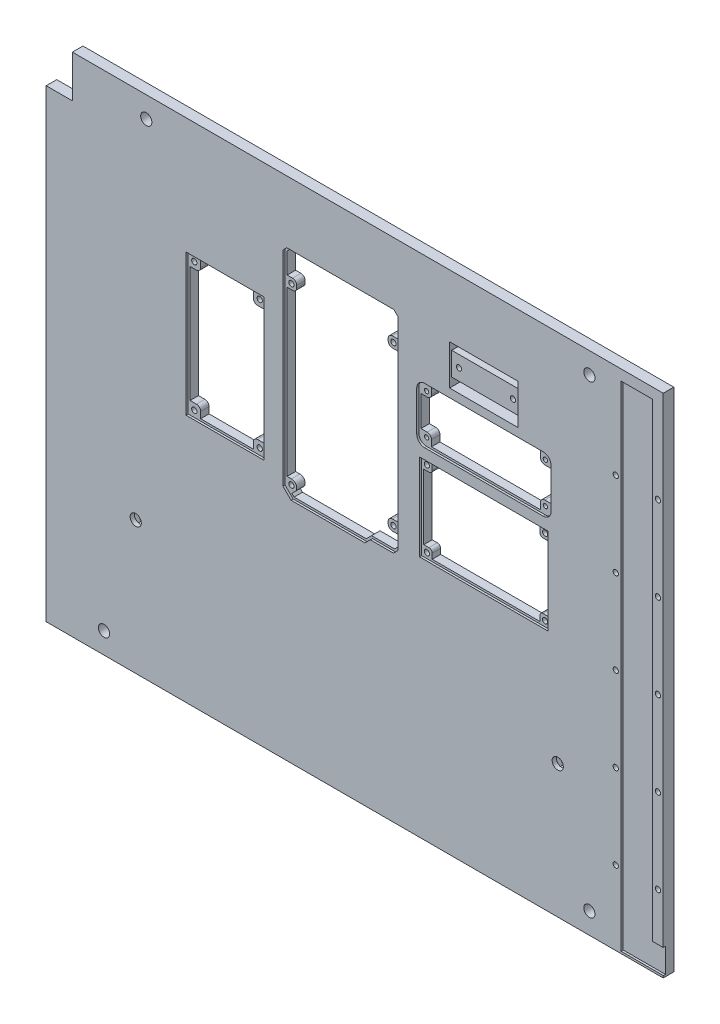
SolidWorks part; units mm, degrees
ref_plane "Front Plane" through (0, 0, 0) normal (0, 0, 1) x (1, 0, 0)
ref_plane "Top Plane" through (0, 0, 0) normal (0, 1, 0) x (1, 0, 0)
ref_plane "Right Plane" through (0, 0, 0) normal (1, 0, 0) x (0, 0, -1)
sketch "Sketch1" plane through (0, 0, 0) normal (0, 0, 1) x (1, 0, 0)
  line L1 (0, 0) -> (300, 0)
  line L2 (0, 0) -> (0, 220)
  line L3 (0, 220) -> (300, 220)
  line L4 (300, 0) -> (300, 220)
  dimension "D1" = 220
  dimension "D2" = 300
extrude "Boss-Extrude1" add sketch "Sketch1" along normal blind 5
sketch "Sketch5" plane through (0, 220, 0) normal (0, 1, 0) x (1, 0, 0)
  line L0 (20, 0) -> (0, 0) construction
  line L1 (20, 0) -> (300, 0)
  line L2 (20, 0) -> (20, -5)
  line L3 (20, -5) -> (300, -5)
  line L4 (300, 0) -> (300, -5)
  line L5 (300, -5) -> (300, 0) construction
  line L6 (20, -5) -> (0, -5) construction
  line L7 (0, -5) -> (0, 0) construction
  dimension "D1" = 20
extrude "Boss-Extrude3" add sketch "Sketch5" along normal blind 20
sketch "Sketch2" plane through (0, 0, 5) normal (0, 0, 1) x (1, 0, 0)
  line L11 (20, 240) -> (300, 240) construction
  line L18 (215, 187) -> (215, 161.6) construction
  line L19 (186.855, 187) -> (243.145, 187)
  line L20 (183.685, 183.83) -> (183.685, 164.77)
  line L21 (186.855, 161.6) -> (243.145, 161.6)
  line L22 (246.315, 183.83) -> (246.315, 164.77)
  line L23 (183.685, 174.3) -> (246.315, 174.3) construction
  line L24 (199.25, 201) -> (230.75, 201) construction
  line L25 (199.25, 192) -> (230.75, 192)
  line L26 (199.25, 192) -> (199.25, 210)
  line L27 (199.25, 210) -> (230.75, 210)
  line L28 (230.75, 192) -> (230.75, 210)
  line L29 (215, 210) -> (215, 192) construction
  line L37 (300, 0) -> (300, 240) construction
  arc A17 (243.145, 187) -> (246.315, 183.83) centre (243.145, 183.83) cw
  arc A18 (246.315, 164.77) -> (243.145, 161.6) centre (243.145, 164.77) cw
  arc A19 (186.855, 161.6) -> (183.685, 164.77) centre (186.855, 164.77) cw
  arc A20 (183.685, 183.83) -> (186.855, 187) centre (186.855, 183.83) cw
  circle A21 centre (186.865, 183.82) radius 1.25
  circle A22 centre (243.135, 183.82) radius 1.25
  circle A23 centre (243.135, 164.78) radius 1.25
  circle A24 centre (186.865, 164.78) radius 1.25
  circle A25 centre (202.2, 201) radius 1.5
  circle A26 centre (227.8, 201) radius 1.5
  point P44 (246.315, 187)
  point P49 (183.685, 161.6)
  point P52 (183.685, 187)
  line B0 (171.9216, 110.94) -> (173.685, 112.7034)
  line B1 (173.685, 112.7034) -> (173.685, 208.476)
  line B2 (173.685, 208.476) -> (172.161, 210)
  line B3 (172.161, 210) -> (121.7928, 210)
  line B4 (121.7928, 210) -> (120.2688, 208.476)
  line B5 (120.2688, 208.476) -> (120.2688, 111.956)
  line B6 (120.2688, 111.956) -> (123.8248, 108.4)
  line B7 (123.8248, 108.4) -> (158.445, 108.4)
  line B8 (158.445, 108.4) -> (160.985, 110.94)
  line B9 (160.985, 110.94) -> (171.9216, 110.94)
  circle B10 centre (122.8088, 113.2514) radius 1.5621
  circle B11 centre (122.8088, 195.8776) radius 1.5621
  circle B12 centre (171.145, 195.8776) radius 1.5621
  circle B13 centre (171.145, 120.7444) radius 1.5621
  line B14 (74.2688, 151.4) -> (110.2688, 151.4) construction
  line B15 (74.2688, 118.4) -> (74.2688, 184.4)
  line B16 (74.2688, 118.4) -> (110.2688, 118.4)
  line B17 (110.2688, 118.4) -> (110.2688, 184.4)
  line B18 (74.2688, 184.4) -> (110.2688, 184.4)
  line B19 (92.2688, 118.4) -> (92.2688, 184.4) construction
  circle B20 centre (76.7688, 120.9) radius 1.6
  circle B21 centre (76.7688, 181.9) radius 1.6
  circle B22 centre (107.7688, 181.9) radius 1.6
  circle B23 centre (107.7688, 120.9) radius 1.6
  line B24 (275, 12.5) -> (275, 0)
  line B25 (275, 240) -> (300, 240)
  line B26 (275, 240) -> (275, 12.5)
  line B27 (275, 12.5) -> (300, 12.5) construction
  line B28 (295, 217.7) -> (280, 217.7) construction
  line B29 (295, 12.5) -> (295, 217.7) construction
  line B30 (280, 12.5) -> (295, 12.5) construction
  line B31 (280, 217.7) -> (280, 12.5) construction
  line B32 (300, 240) -> (300, 12.5)
  line B33 (275, 0) -> (300, 0)
  line B34 (300, 0) -> (300, 12.5)
  circle B35 centre (297.5, 35.1) radius 1.25
  circle B36 centre (297.5, 75.1) radius 1.25
  circle B37 centre (297.5, 115.1) radius 1.25
  circle B38 centre (297.5, 155.1) radius 1.25
  circle B39 centre (297.5, 195.1) radius 1.25
  circle B40 centre (277.5, 195.1) radius 1.25
  circle B41 centre (277.5, 155.1) radius 1.25
  circle B42 centre (277.5, 75.1) radius 1.25
  circle B43 centre (277.5, 115.1) radius 1.25
  circle B44 centre (277.5, 35.1) radius 1.25
  dimension "D37" = 3.17
  dimension "D38" = 2.5
  dimension "D39" = 3.18
  dimension "D40" = 3.18
  dimension "D45" = 3
  dimension "D1" = 30
  dimension "D2" = 10
  dimension "D5" = 10
  dimension "D6" = 5
  dimension "D7" = 25.6
  dimension "D8" = 10
  dimension "D35" = 62.63
  dimension "D36" = 25.4
  dimension "D41" = 85
  dimension "D43" = 31.5
  dimension "D44" = 18
sketch_block_instance "Block1-1"
sketch_block "Block1" parameters "D8"=1.5621, "D15"=1.5621, "D16"=1.5621, "D19"=3.1242, "D1"=2.54, "D2"=2.54, "D3"=9.8044, "D4"=2.54, "D5"=2.54, "D6"=14.1224, "D7"=14.1224, "D9"=53.4162, "D10"=101.6, "D11"=99.06, "D12"=3.5921, "D13"=5.0289, "D14"=2.4939, "D17"=2.1553, "D18"=2.1553, "D20"=34.6202, "D21"=10.9366, "D22"=4.8514, "D23"=1.524, "D24"=3.556, "D25"=1.524
sketch_block_instance "Block4-1"
sketch_block "Block4" parameters "D3"=3.2, "D1"=66, "D2"=36, "D4"=2.5, "D5"=2.5
sketch_block_instance "Block5-1"
sketch_block "Block5" parameters "D1"=25, "D2"=227.5, "D3"=12.5
sketch "Sketch7" plane through (0, 0, 5) normal (0, 0, 1) x (1, 0, 0)
  line L0 (295, 12.5) -> (300, 12.5)
  line L1 (300, 12.5) -> (300, 1)
  line L2 (300, 0) -> (300, 12.5) construction
  line L187 (119.7688, 111.7489) -> (123.6177, 107.9)
  line L188 (123.6177, 107.9) -> (158.6521, 107.9)
  line L189 (158.6521, 107.9) -> (161.1921, 110.44)
  line L190 (161.1921, 110.44) -> (172.1287, 110.44)
  line L191 (172.1287, 110.44) -> (174.185, 112.4963)
  line L192 (174.185, 112.4963) -> (174.185, 208.6831)
  line L193 (174.185, 208.6831) -> (172.3681, 210.5)
  line L194 (119.7688, 208.6831) -> (119.7688, 111.7489)
  line L195 (121.5857, 210.5) -> (119.7688, 208.6831)
  line L196 (172.3681, 210.5) -> (121.5857, 210.5)
  line L197 (119.7688, 111.7489) -> (123.6177, 107.9)
  line L198 (123.6177, 107.9) -> (158.6521, 107.9)
  line L199 (158.6521, 107.9) -> (161.1921, 110.44)
  line L200 (161.1921, 110.44) -> (172.1287, 110.44)
  line L201 (172.1287, 110.44) -> (174.185, 112.4963)
  line L202 (174.185, 112.4963) -> (174.185, 208.6831)
  line L203 (174.185, 208.6831) -> (172.3681, 210.5)
  line L204 (119.7688, 208.6831) -> (119.7688, 111.7489)
  line L205 (121.5857, 210.5) -> (119.7688, 208.6831)
  line L206 (172.3681, 210.5) -> (121.5857, 210.5)
  line L211 (110.7688, 117.9) -> (110.7688, 184.9)
  line L212 (73.7688, 117.9) -> (110.7688, 117.9)
  line L213 (73.7688, 184.9) -> (73.7688, 117.9)
  line L214 (110.7688, 184.9) -> (73.7688, 184.9)
  line L215 (110.7688, 117.9) -> (110.7688, 184.9)
  line L216 (73.7688, 117.9) -> (110.7688, 117.9)
  line L217 (73.7688, 184.9) -> (73.7688, 117.9)
  line L218 (110.7688, 184.9) -> (73.7688, 184.9)
  line L223 (243.145, 187.5) -> (186.855, 187.5)
  line L224 (246.815, 164.77) -> (246.815, 183.83)
  line L225 (186.855, 161.1) -> (243.145, 161.1)
  line L226 (183.185, 183.83) -> (183.185, 164.77)
  line L227 (243.145, 187.5) -> (186.855, 187.5)
  line L228 (246.815, 164.77) -> (246.815, 183.83)
  line L229 (186.855, 161.1) -> (243.145, 161.1)
  line L230 (183.185, 183.83) -> (183.185, 164.77)
  line L231 (300, 1) -> (280, 1)
  line L232 (184.5, 156.1) -> (245.5, 156.1)
  line L233 (184.5, 156.1) -> (184.5, 115.1)
  line L234 (184.5, 115.1) -> (245.5, 115.1)
  line L235 (198.75, 210.5) -> (198.75, 191.5)
  line L236 (198.75, 191.5) -> (231.25, 191.5)
  line L237 (231.25, 191.5) -> (231.25, 210.5)
  line L238 (231.25, 210.5) -> (198.75, 210.5)
  line L239 (198.75, 210.5) -> (198.75, 191.5)
  line L240 (198.75, 191.5) -> (231.25, 191.5)
  line L241 (231.25, 191.5) -> (231.25, 210.5)
  line L242 (231.25, 210.5) -> (198.75, 210.5)
  line L243 (245.5, 156.1) -> (245.5, 115.1)
  line L244 (184.5, 156.1) -> (245.5, 115.1) construction
  line L245 (184.5, 115.1) -> (245.5, 156.1) construction
  line L247 (280, 1) -> (280, 235)
  line L249 (295, 12.5) -> (295, 235)
  line L250 (295, 12.5) -> (295, 217.7) construction
  line L251 (295, 235) -> (280, 235)
  line L252 (275, 240) -> (300, 240) construction
  line L253 (280, 217.7) -> (280, 12.5) construction
  line L254 (275, 0) -> (300, 0) construction
  line L256 (215, 156.1) -> (215, 115.1) construction
  line L257 (215, 187) -> (215, 161.6) construction
  arc A11 (246.815, 183.83) -> (243.145, 187.5) centre (243.145, 183.83) ccw
  arc A12 (243.145, 161.1) -> (246.815, 164.77) centre (243.145, 164.77) ccw
  arc A13 (183.185, 164.77) -> (186.855, 161.1) centre (186.855, 164.77) ccw
  arc A14 (186.855, 187.5) -> (183.185, 183.83) centre (186.855, 183.83) ccw
  arc A15 (246.815, 183.83) -> (243.145, 187.5) centre (243.145, 183.83) ccw
  arc A16 (243.145, 161.1) -> (246.815, 164.77) centre (243.145, 164.77) ccw
  arc A17 (183.185, 164.77) -> (186.855, 161.1) centre (186.855, 164.77) ccw
  arc A18 (186.855, 187.5) -> (183.185, 183.83) centre (186.855, 183.83) ccw
  point P0 (215, 135.6)
  dimension "D5" = 5
  dimension "D6" = 41
  dimension "D7" = 5
  dimension "D8" = 1
  dimension "D9" = 61
  dimension "D1" = 0.5
  dimension "D2" = 0.5
  dimension "D3" = 0.5
  dimension "D4" = 0.5
extrude "Cut-Extrude3" cut sketch "Sketch7" against normal blind 1
sketch "Sketch9" plane through (0, 0, 5) normal (0, 0, 1) x (1, 0, 0)
  line L0 (79.7688, 183.9) -> (92.2688, 183.9)
  line L1 (73.7688, 184.9) -> (79.7688, 184.9) construction
  line L2 (73.7688, 184.9) -> (73.7688, 178.9) construction
  line L3 (73.7688, 178.9) -> (79.7688, 178.9) construction
  line L4 (79.7688, 184.9) -> (79.7688, 178.9) construction
  line L5 (92.2688, 118.4) -> (92.2688, 184.4) construction
  line L6 (74.7688, 178.9) -> (74.7688, 123.9)
  line L7 (74.2688, 151.4) -> (110.2688, 151.4) construction
  line L8 (73.7688, 184.9) -> (73.7688, 117.9) construction
  line L9 (110.7688, 184.9) -> (73.7688, 184.9) construction
  line L10 (79.7688, 183.9) -> (79.7688, 180.9)
  line L11 (77.7688, 178.9) -> (74.7688, 178.9)
  line L12 (92.2688, 184.9) -> (92.2688, 117.9) construction
  line L13 (110.7688, 184.9) -> (73.7688, 184.9) construction
  line L14 (73.7688, 117.9) -> (110.7688, 117.9) construction
  line L15 (74.2688, 151.4) -> (110.2688, 151.4) construction
  line L16 (74.2688, 118.4) -> (74.2688, 184.4) construction
  line L17 (92.2688, 176.5163) -> (92.2688, 184.9) construction
  line L18 (71.2994, 151.4) -> (74.2688, 151.4) construction
  line L19 (109.7688, 178.9) -> (109.7688, 123.9)
  line L20 (106.7688, 178.9) -> (109.7688, 178.9)
  line L21 (104.7688, 183.9) -> (104.7688, 180.9)
  line L22 (104.7688, 183.9) -> (92.2688, 183.9)
  line L23 (77.7688, 123.9) -> (74.7688, 123.9)
  line L24 (79.7688, 118.9) -> (79.7688, 121.9)
  line L25 (79.7688, 118.9) -> (92.2688, 118.9)
  line L26 (106.7688, 123.9) -> (109.7688, 123.9)
  line L27 (104.7688, 118.9) -> (104.7688, 121.9)
  line L28 (104.7688, 118.9) -> (92.2688, 118.9)
  line L29 (215, 156.1) -> (215, 115.1) construction
  line L34 (245.5, 156.1) -> (184.5, 156.1) construction
  line L35 (120.3088, 193.3776) -> (125.3088, 193.3776) construction
  line L36 (120.3088, 193.3776) -> (120.3088, 198.3776) construction
  line L37 (120.3088, 198.3776) -> (125.3088, 198.3776) construction
  line L38 (125.3088, 193.3776) -> (125.3088, 198.3776) construction
  line L39 (120.3088, 193.3776) -> (125.3088, 198.3776) construction
  line L40 (120.3088, 198.3776) -> (125.3088, 193.3776) construction
  line L41 (173.645, 193.3776) -> (168.645, 193.3776) construction
  line L42 (173.645, 193.3776) -> (173.645, 198.3776) construction
  line L43 (173.645, 198.3776) -> (168.645, 198.3776) construction
  line L44 (168.645, 193.3776) -> (168.645, 198.3776) construction
  line L45 (173.645, 193.3776) -> (168.645, 198.3776) construction
  line L46 (173.645, 198.3776) -> (168.645, 193.3776) construction
  line L47 (173.645, 118.2444) -> (168.645, 118.2444) construction
  line L48 (173.645, 118.2444) -> (173.645, 123.2444) construction
  line L49 (173.645, 123.2444) -> (168.645, 123.2444) construction
  line L50 (168.645, 118.2444) -> (168.645, 123.2444) construction
  line L51 (173.645, 118.2444) -> (168.645, 123.2444) construction
  line L52 (173.645, 123.2444) -> (168.645, 118.2444) construction
  line L57 (184.5, 115.1) -> (245.5, 115.1) construction
  line L58 (184.5, 135.6) -> (245.5, 135.6) construction
  line L59 (184.5, 156.1) -> (184.5, 115.1) construction
  line L60 (245.5, 115.1) -> (245.5, 156.1) construction
  line L61 (185.5, 120.1) -> (185.5, 151.1)
  line L62 (185.5, 151.1) -> (187.9668, 151.1)
  line L63 (189.5, 152.6332) -> (189.5, 155.1)
  line L64 (189.5, 155.1) -> (240.5, 155.1)
  line L65 (245.5, 156.1) -> (184.5, 156.1) construction
  line L66 (240.5, 152.6332) -> (240.5, 155.1)
  line L67 (244.5, 151.1) -> (242.0332, 151.1)
  line L68 (244.5, 120.1) -> (244.5, 151.1)
  line L69 (244.5, 120.1) -> (242.0332, 120.1)
  line L70 (240.5, 118.5668) -> (240.5, 116.1)
  line L71 (189.5, 116.1) -> (240.5, 116.1)
  line L72 (189.5, 118.5668) -> (189.5, 116.1)
  line L73 (185.5, 120.1) -> (187.9668, 120.1)
  line L108 (173.185, 208.2689) -> (173.185, 198.3776)
  line L109 (173.185, 198.3776) -> (170.645, 198.3776)
  line L110 (168.645, 196.3776) -> (168.645, 195.3776)
  line L111 (170.645, 193.3776) -> (173.185, 193.3776)
  line L112 (173.185, 193.3776) -> (173.185, 123.2444)
  line L113 (173.185, 123.2444) -> (170.645, 123.2444)
  line L114 (168.645, 121.2444) -> (168.645, 120.2444)
  line L115 (170.645, 118.2444) -> (173.185, 118.2444)
  line L116 (173.185, 118.2444) -> (173.185, 112.9105)
  line L117 (123.0124, 109.9195) -> (124.5766, 111.4836)
  line L118 (121.9999, 209.5) -> (120.7688, 208.2689)
  line L119 (171.9539, 209.5) -> (121.9999, 209.5)
  line L120 (173.185, 208.2689) -> (171.9539, 209.5)
  line L121 (173.185, 112.9105) -> (173.185, 208.2689)
  line L122 (171.7145, 111.44) -> (173.185, 112.9105)
  line L123 (160.7779, 111.44) -> (171.7145, 111.44)
  line L124 (158.2379, 108.9) -> (160.7779, 111.44)
  line L125 (124.0319, 108.9) -> (158.2379, 108.9)
  line L126 (120.7688, 112.1631) -> (124.0319, 108.9)
  line L127 (120.7688, 208.2689) -> (120.7688, 112.1631)
  line L128 (121.9999, 209.5) -> (120.7688, 208.2689)
  line L129 (171.9539, 209.5) -> (121.9999, 209.5)
  line L130 (173.185, 208.2689) -> (171.9539, 209.5)
  line L131 (173.185, 112.9105) -> (173.185, 208.2689) construction
  line L132 (171.7145, 111.44) -> (173.185, 112.9105)
  line L133 (160.7779, 111.44) -> (171.7145, 111.44)
  line L134 (158.2379, 108.9) -> (160.7779, 111.44)
  line L135 (124.0319, 108.9) -> (158.2379, 108.9)
  line L136 (120.7688, 112.1631) -> (124.0319, 108.9) construction
  line L137 (120.7688, 208.2689) -> (120.7688, 112.1631) construction
  line L138 (120.7688, 115.7514) -> (122.8088, 115.7514)
  line L139 (123.0124, 109.9195) -> (124.0319, 108.9)
  line L140 (120.7688, 115.7514) -> (120.7688, 193.3776)
  line L141 (120.7688, 193.3776) -> (123.3088, 193.3776)
  line L142 (125.3088, 195.3776) -> (125.3088, 196.3776)
  line L143 (123.3088, 198.3776) -> (120.7688, 198.3776)
  line L144 (120.7688, 198.3776) -> (120.7688, 208.2689)
  line L145 (231.25, 191.5) -> (231.25, 210.5) construction
  line L146 (198.75, 210.5) -> (231.25, 210.5)
  line L147 (198.75, 210.5) -> (198.75, 206.5)
  line L148 (198.75, 206.5) -> (231.25, 206.5)
  line L149 (231.25, 210.5) -> (231.25, 206.5)
  line L150 (230.75, 192) -> (230.75, 210) construction
  line L151 (198.75, 191.5) -> (230.75, 191.5)
  line L152 (198.75, 191.5) -> (198.75, 195.5)
  line L153 (198.75, 195.5) -> (230.75, 195.5)
  line L154 (230.75, 191.5) -> (230.75, 195.5)
  line L155 (215, 187) -> (215, 189.4399) construction
  line L156 (183.685, 174.3) -> (181.2405, 174.3) construction
  line L157 (183.685, 183.83) -> (183.685, 164.77) construction
  line L158 (184.185, 167.1) -> (184.185, 181.5)
  line L159 (183.685, 174.3) -> (246.315, 174.3) construction
  line L160 (184.185, 181.5) -> (187.185, 181.5)
  line L161 (189.185, 183.5) -> (189.185, 186.5)
  line L162 (189.185, 186.5) -> (240.815, 186.5)
  line L163 (215, 187) -> (215, 161.6) construction
  line L164 (186.855, 187) -> (243.145, 187) construction
  line L165 (189.185, 162.1) -> (240.815, 162.1)
  line L166 (189.185, 165.1) -> (189.185, 162.1)
  line L167 (184.185, 167.1) -> (187.185, 167.1)
  line L168 (240.815, 165.1) -> (240.815, 162.1)
  line L169 (245.815, 167.1) -> (242.815, 167.1)
  line L170 (245.815, 167.1) -> (245.815, 181.5)
  line L171 (245.815, 181.5) -> (242.815, 181.5)
  line L172 (240.815, 183.5) -> (240.815, 186.5)
  circle A0 centre (76.7688, 181.9) radius 1.25
  arc A1 (79.7688, 180.9) -> (77.7688, 178.9) centre (77.7688, 180.9) cw
  arc A2 (104.7688, 180.9) -> (106.7688, 178.9) centre (106.7688, 180.9) ccw
  arc A3 (79.7688, 121.9) -> (77.7688, 123.9) centre (77.7688, 121.9) ccw
  arc A4 (104.7688, 121.9) -> (106.7688, 123.9) centre (106.7688, 121.9) cw
  circle A5 centre (107.7688, 181.9) radius 1.25
  circle A6 centre (107.7688, 120.9) radius 1.25
  circle A7 centre (76.7688, 120.9) radius 1.25
  circle A8 centre (297.5, 35.1) radius 1.25 construction
  circle A9 centre (277.5, 35.1) radius 1.25 construction
  circle A10 centre (277.5, 75.1) radius 1.25 construction
  circle A11 centre (297.5, 75.1) radius 1.25 construction
  circle A12 centre (297.5, 115.1) radius 1.25 construction
  circle A13 centre (277.5, 115.1) radius 1.25 construction
  circle A14 centre (277.5, 155.1) radius 1.25 construction
  circle A15 centre (297.5, 155.1) radius 1.25 construction
  circle A16 centre (297.5, 195.1) radius 1.25 construction
  circle A17 centre (277.5, 195.1) radius 1.25 construction
  circle A18 centre (297.5, 35.1) radius 1.25
  circle A19 centre (277.5, 35.1) radius 1.25
  circle A20 centre (277.5, 75.1) radius 1.25
  circle A21 centre (297.5, 75.1) radius 1.25
  circle A22 centre (297.5, 115.1) radius 1.25
  circle A23 centre (277.5, 115.1) radius 1.25
  circle A24 centre (277.5, 155.1) radius 1.25
  circle A25 centre (297.5, 155.1) radius 1.25
  circle A26 centre (297.5, 195.1) radius 1.25
  circle A27 centre (277.5, 195.1) radius 1.25
  arc A28 (122.8088, 115.7514) -> (124.5766, 111.4836) centre (122.8088, 113.2514) cw
  circle A29 centre (122.8088, 113.2514) radius 1.5621 construction
  arc A30 (170.645, 118.2444) -> (168.645, 120.2444) centre (170.645, 120.2444) cw
  arc A31 (168.645, 121.2444) -> (170.645, 123.2444) centre (170.645, 121.2444) cw
  arc A32 (168.645, 195.3776) -> (170.645, 193.3776) centre (170.645, 195.3776) ccw
  arc A33 (168.645, 196.3776) -> (170.645, 198.3776) centre (170.645, 196.3776) cw
  arc A34 (125.3088, 195.3776) -> (123.3088, 193.3776) centre (123.3088, 195.3776) cw
  arc A35 (125.3088, 196.3776) -> (123.3088, 198.3776) centre (123.3088, 196.3776) ccw
  circle A36 centre (122.8088, 113.2514) radius 1.25
  circle A37 centre (171.145, 120.7444) radius 1.25
  circle A38 centre (122.8088, 195.8776) radius 1.25
  circle A39 centre (171.145, 195.8776) radius 1.25
  circle A40 centre (202.2, 201) radius 1.25
  circle A41 centre (227.8, 201) radius 1.25
  arc A42 (189.185, 183.5) -> (187.185, 181.5) centre (187.185, 183.5) cw
  arc A43 (189.185, 165.1) -> (187.185, 167.1) centre (187.185, 165.1) ccw
  arc A44 (240.815, 165.1) -> (242.815, 167.1) centre (242.815, 165.1) cw
  arc A45 (240.815, 183.5) -> (242.815, 181.5) centre (242.815, 183.5) ccw
  circle A46 centre (186.865, 183.82) radius 1.025
  circle A47 centre (186.865, 164.78) radius 1.025
  circle A48 centre (243.145, 164.77) radius 1.025
  circle A49 centre (243.135, 183.82) radius 1.025
  circle A50 centre (243.135, 183.82) radius 1.25 construction
  circle A51 centre (186.865, 164.78) radius 1.25 construction
  circle A52 centre (186.865, 183.82) radius 1.25 construction
  circle A53 centre (187, 153.6) radius 1.25
  arc A54 (189.5, 152.6332) -> (187.9668, 151.1) centre (187.9668, 152.6332) cw
  arc A55 (240.5, 152.6332) -> (242.0332, 151.1) centre (242.0332, 152.6332) ccw
  arc A56 (240.5, 118.5668) -> (242.0332, 120.1) centre (242.0332, 118.5668) cw
  arc A57 (189.5, 118.5668) -> (187.9668, 120.1) centre (187.9668, 118.5668) ccw
  circle A58 centre (243, 153.6) radius 1.25
  circle A59 centre (243, 117.6) radius 1.25
  circle A60 centre (187, 117.6) radius 1.25
  point P15 (86.0188, 183.9)
  point P44 (74.7688, 151.4)
  point P50 (109.7688, 151.4)
  point P90 (171.145, 195.8776)
  point P95 (171.145, 120.7444)
  point P97 (122.8088, 195.8776)
  point P107 (122.8088, 113.2514)
  point P198 (189.185, 181.5)
  point P205 (184.185, 174.3)
  point P206 (215, 162.1)
  point P215 (215, 186.5)
  point P254 (215, 155.1)
  point P260 (244.5, 135.6)
  point P269 (185.5, 135.6)
  dimension "D5" = 2.5
  dimension "D6" = 2
  dimension "D7" = 5
  dimension "D10" = 2.5
  dimension "D16" = 2.5
  dimension "D17" = 2
  dimension "D18" = 2.5
  dimension "D19" = 2.5
  dimension "D20" = 2.5
  dimension "D21" = 2.5
  dimension "D24" = 2.5
  dimension "D25" = 2.5
  dimension "D30" = 2
  dimension "D31" = 2.05
  dimension "D32" = 2.05
  dimension "D33" = 2.05
  dimension "D34" = 2.05
  dimension "D35" = 2.5
  dimension "D36" = 2.5
  dimension "D37" = 2.5
  dimension "D42" = 1.5332
  dimension "D1" = 6
  dimension "D2" = 6
  dimension "D3" = 1
  dimension "D4" = 1
  dimension "D8" = 5
  dimension "D9" = 0.5
  dimension "D11" = 5
  dimension "D12" = 5
  dimension "D13" = 5
  dimension "D14" = 5
  dimension "D15" = 2.5
  dimension "D22" = 4
  dimension "D23" = 4
  dimension "D26" = 0.5
  dimension "D27" = 0.5
  dimension "D28" = 5
  dimension "D29" = 5
  dimension "D38" = 5
  dimension "D39" = 5
  dimension "D40" = 1
  dimension "D41" = 1
extrude "Cut-Extrude4" cut sketch "Sketch9" against normal blind 5
sketch "Sketch10" plane through (0, 0, 5) normal (0, 0, 1) x (1, 0, 0)
  line L0 (0, 63) -> (300, 63) construction
  line L1 (0, 220) -> (0, 0) construction
  line L2 (300, 240) -> (300, 12.5) construction
  line L3 (0, 10) -> (300, 10) construction
  line L5 (0, 0) -> (300, 0) construction
  line L6 (20, 230) -> (300, 230) construction
  line L7 (20, 240) -> (20, 220) construction
  circle A0 centre (50, 63) radius 2.65
  circle A1 centre (250, 63) radius 2.65
  circle A2 centre (35, 10) radius 2.65
  circle A3 centre (265, 10) radius 2.65
  circle A4 centre (265, 230) radius 2.65
  circle A5 centre (55, 230) radius 2.65
  dimension "D1" = 5.3
  dimension "D3" = 5.3
  dimension "D5" = 200
  dimension "D6" = 63
  dimension "D7" = 5.3
  dimension "D8" = 5.3
  dimension "D9" = 5.3
  dimension "D10" = 5.3
  dimension "D12" = 35
  dimension "D13" = 35
  dimension "D14" = 35
  dimension "D2" = 50
  dimension "D4" = 10
  dimension "D11" = 35
extrude "Cut-Extrude5" cut sketch "Sketch10" against normal blind 10
sketch "Sketch11" plane through (0, 0, 0) normal (0, 0, -1) x (-1, 0, 0)
  line L0 (0, 0) -> (-300, 0) construction
  line L1 (-247.5174, 67.3) -> (-252.4826, 67.3)
  line L2 (-252.4826, 67.3) -> (-254.9652, 63)
  line L3 (-254.9652, 63) -> (-252.4826, 58.7)
  line L4 (-252.4826, 58.7) -> (-247.5174, 58.7)
  line L5 (-247.5174, 58.7) -> (-245.0348, 63)
  line L6 (-245.0348, 63) -> (-247.5174, 67.3)
  line L8 (-47.5174, 67.3) -> (-52.4826, 67.3)
  line L9 (-52.4826, 67.3) -> (-54.9652, 63)
  line L10 (-54.9652, 63) -> (-52.4826, 58.7)
  line L11 (-52.4826, 58.7) -> (-47.5174, 58.7)
  line L12 (-47.5174, 58.7) -> (-45.0348, 63)
  line L13 (-45.0348, 63) -> (-47.5174, 67.3)
  circle A0 centre (-250, 63) radius 4.3 construction
  circle A1 centre (-50, 63) radius 4.3 construction
  dimension "D1" = 8.6
  dimension "D2" = 8.6
extrude "Cut-Extrude6" cut sketch "Sketch11" against normal blind 3
sketch "Sketch12" plane through (0, 0, 5) normal (0, 0, 1) x (1, 0, 0)
  line L1 (-7.5879, 452.3851) -> (7.5879, 452.3851)
  line L2 (-7.5879, 452.3851) -> (-7.5879, -12.3851)
  line L3 (-7.5879, -12.3851) -> (7.5879, -12.3851)
  line L4 (7.5879, 452.3851) -> (7.5879, -12.3851)
  line L5 (-7.5879, 452.3851) -> (7.5879, -12.3851) construction
  line L6 (-7.5879, -12.3851) -> (7.5879, 452.3851) construction
  point P0 (0, 220)
extrude "ForPrintAdjust" cut sketch "Sketch12" against normal blind 5
